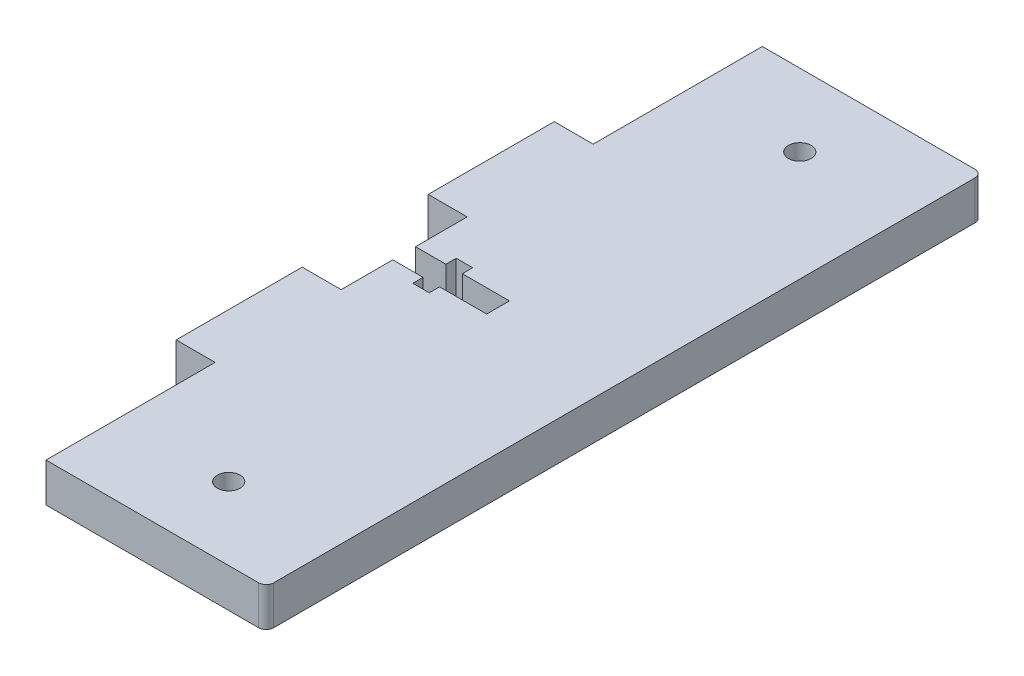
SolidWorks part; units mm, degrees
ref_plane "Front Plane" through (0, 0, 0) normal (0, 0, 1) x (1, 0, 0)
ref_plane "Top Plane" through (0, 0, 0) normal (0, 1, 0) x (1, 0, 0)
ref_plane "Right Plane" through (0, 0, 0) normal (1, 0, 0) x (0, 0, -1)
sketch "Sketch3" plane through (0, 0, 0) normal (0, 1, 0) x (1, 0, 0)
  line L0 (-15.9909, -2.6354) -> (-15.9909, -9.4369)
  line L1 (-15.9909, -2.6354) -> (-11.9959, -2.6354)
  line L2 (-11.9959, 0.3616) -> (-15.9909, 0.3616)
  line L3 (-11.9959, 1.7206) -> (-11.9959, 0.3616)
  line L4 (-9.8289, 0.3616) -> (-9.8289, 1.7206)
  line L5 (-9.8289, 1.7206) -> (-11.9959, 1.7206)
  line L6 (-11.9959, -2.6354) -> (-11.9959, -3.9944)
  line L7 (-9.8289, -3.9944) -> (-9.8289, -2.6354)
  line L8 (-11.9959, -3.9944) -> (-9.8289, -3.9944)
  line L9 (-3.6219, -2.6354) -> (-3.6219, 0.3616)
  line L10 (-3.6219, 0.3616) -> (-9.8289, 0.3616)
  line L11 (-9.8289, -2.6354) -> (-3.6219, -2.6354)
  line L12 (-15.9909, 0.3616) -> (-15.9909, 7.1631)
  line L13 (-15.9909, -48.3169) -> (12.0091, -48.3169)
  line L14 (-15.9909, 46.0431) -> (12.0091, 46.0431)
  line L15 (-15.9909, -9.4369) -> (-21.1209, -9.4369)
  line L16 (-15.9909, 7.1631) -> (-21.1209, 7.1631)
  line L65 (13.0091, -47.3169) -> (13.0091, 45.0431)
  line L66 (-21.1209, -9.4369) -> (-21.1209, -26.0369)
  line L67 (-21.1209, 7.1631) -> (-21.1209, 23.7631)
  line L68 (-21.1209, -26.0369) -> (-15.9909, -26.0369)
  line L69 (-15.9909, -26.0369) -> (-15.9909, -48.3169)
  line L70 (-21.1209, 23.7631) -> (-15.9909, 23.7631)
  line L71 (-15.9909, 23.7631) -> (-15.9909, 46.0431)
  circle A0 centre (-1.4909, -38.7509) radius 1.5
  circle A1 centre (-1.4909, 36.4771) radius 1.5
  arc A2 (13.0091, -47.3169) -> (12.0091, -48.3169) centre (12.0091, -47.3169) cw
  arc A3 (12.0091, 46.0431) -> (13.0091, 45.0431) centre (12.0091, 45.0431) cw
  point P24 (13.0091, -48.3169)
  point P27 (13.0091, 46.0431)
  dimension "D5" = 3
  dimension "D6" = 3
  dimension "D17" = 3.995
  dimension "D18" = 3.995
  dimension "D23" = 29
  dimension "D28" = 1
  dimension "D29" = 1
  dimension "D30" = 5.13
  dimension "D1" = 2.997
  dimension "D2" = 6.8015
  dimension "D3" = 6.8015
  dimension "D4" = 5.13
  dimension "D7" = 29
  dimension "D8" = 5.13
  dimension "D9" = 16.6
  dimension "D10" = 16.6
  dimension "D11" = 22.28
  dimension "D12" = 22.28
  dimension "D13" = 14.5
  dimension "D14" = 14.5
  dimension "D15" = 9.566
  dimension "D16" = 9.566
  dimension "D19" = 2.167
  dimension "D20" = 94.36
  dimension "D21" = 2.167
  dimension "D22" = 6.207
  dimension "D24" = 6.207
  dimension "D25" = 2.997
  dimension "D26" = 90
  dimension "D27" = 90
extrude "Boss-Extrude1" add sketch "Sketch3" along normal blind 5.13
equation "\"D13@Sketch3\" = \"D7@Sketch3\"/2"
equation "\"D14@Sketch3\" = \"D7@Sketch3\"/2"
equation "\"D23@Sketch3\" = \"D7@Sketch3\""
